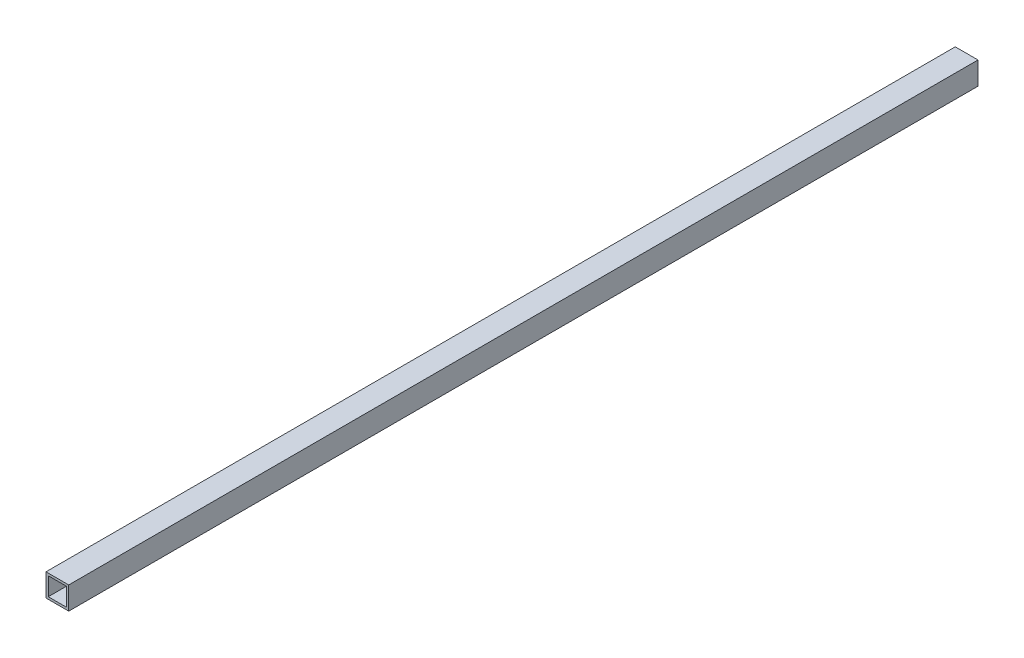
SolidWorks part; units mm, degrees
ref_plane "Front" through (0, 0, 0) normal (0, 0, 1) x (1, 0, 0)
ref_plane "Top" through (0, 0, 0) normal (0, 1, 0) x (1, 0, 0)
ref_plane "Right" through (0, 0, 0) normal (1, 0, 0) x (0, 0, -1)
sketch "Sketch2" plane through (0, 0, 0) normal (0, 0, 1) x (1, 0, 0)
  line L1 (-5, -5) -> (5, -5)
  line L2 (-5, -5) -> (-5, 5)
  line L3 (-5, 5) -> (5, 5)
  line L4 (5, -5) -> (5, 5)
  line L5 (-5, -5) -> (5, 5) construction
  line L6 (-5, 5) -> (5, -5) construction
  point P0 (0, 0)
  dimension "D1" = 10
  dimension "D2" = 10
extrude "Boss-Extrude1" add sketch "Sketch2" along normal blind 400
sketch "Sketch3" plane through (0, 0, 400) normal (0, 0, 1) x (1, 0, 0)
  line L1 (-4, -4) -> (4, -4)
  line L2 (-4, -4) -> (-4, 4)
  line L3 (-4, 4) -> (4, 4)
  line L4 (4, -4) -> (4, 4)
  line L5 (-4, -4) -> (4, 4) construction
  line L6 (-4, 4) -> (4, -4) construction
  point P0 (0, 0)
  dimension "D1" = 8
  dimension "D2" = 8
extrude "Cut-Extrude1" cut sketch "Sketch3" against normal blind 400
